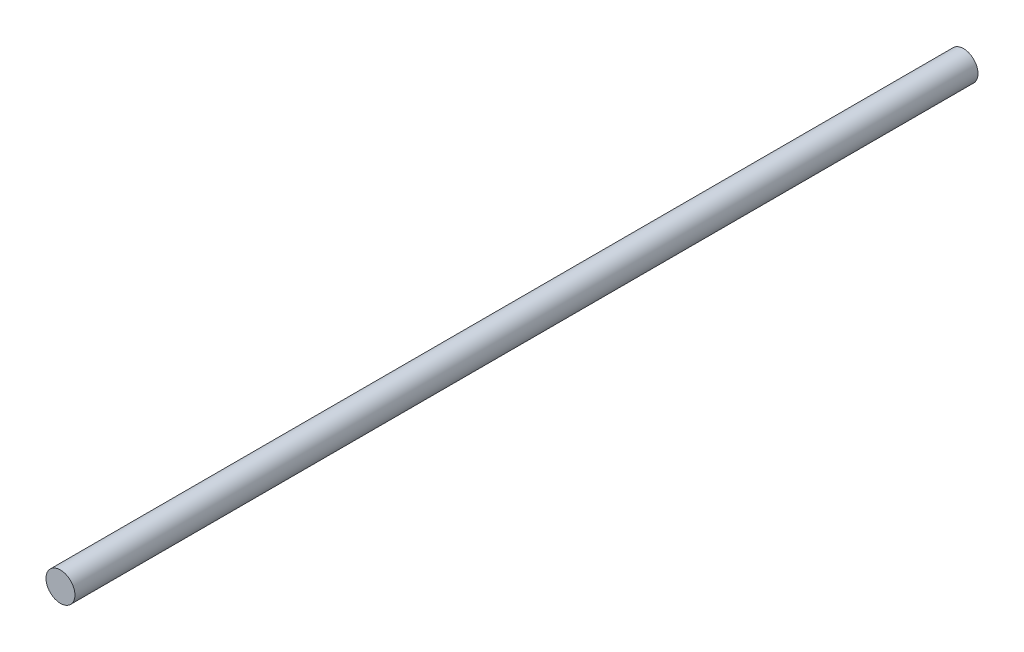
SolidWorks part; units mm, degrees
ref_plane "Front Plane" through (0, 0, 0) normal (0, 0, 1) x (1, 0, 0)
ref_plane "Top Plane" through (0, 0, 0) normal (0, 1, 0) x (1, 0, 0)
ref_plane "Right Plane" through (0, 0, 0) normal (1, 0, 0) x (0, 0, -1)
sketch "Sketch1" plane through (0, 0, 0) normal (0, 0, 1) x (1, 0, 0)
  circle A0 centre (0, 0) radius 0.625
  dimension "D1" = 1.25
extrude "Boss-Extrude1" add sketch "Sketch1" along normal blind 39
